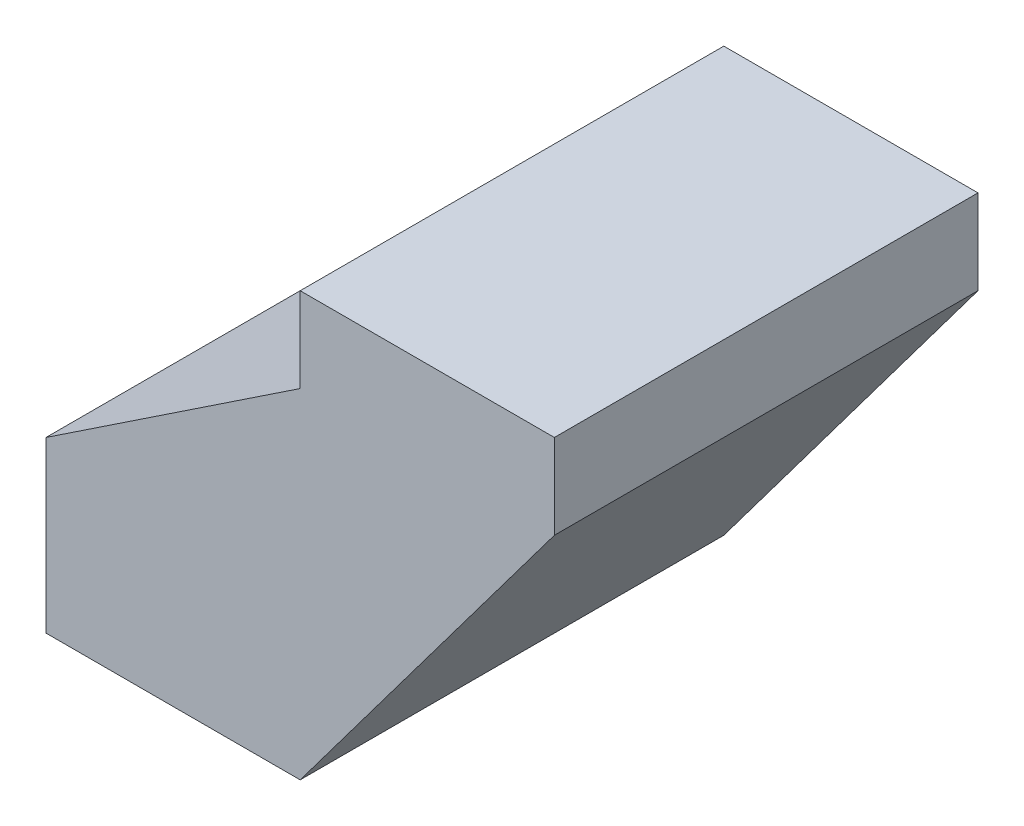
SolidWorks part; units mm, degrees
ref_plane "Front Plane" through (0, 0, 0) normal (0, 0, 1) x (1, 0, 0)
ref_plane "Top Plane" through (0, 0, 0) normal (0, 1, 0) x (1, 0, 0)
ref_plane "Right Plane" through (0, 0, 0) normal (1, 0, 0) x (0, 0, -1)
sketch "Sketch1" plane through (0, 0, 0) normal (0, 0, 1) x (1, 0, 0)
  line L0 (0, 25) -> (15, 25)
  line L1 (15, 25) -> (15, 20)
  line L2 (15, 20) -> (0, 0)
  line L3 (0, 0) -> (-15, 0)
  line L4 (-15, 0) -> (-15, 10)
  line L5 (-15, 10) -> (0, 20)
  line L6 (0, 20) -> (0, 25)
  point P2 (0, 10)
  point P8 (15, 0)
  dimension "D1" = 15
  dimension "D2" = 5
  dimension "D3" = 5
  dimension "D4" = 15
  dimension "D5" = 10
  dimension "D6" = 15
  dimension "D7" = 20
  dimension "D8" = 10
  dimension "D9" = 15
extrude "Boss-Extrude1" add sketch "Sketch1" along normal blind 25
